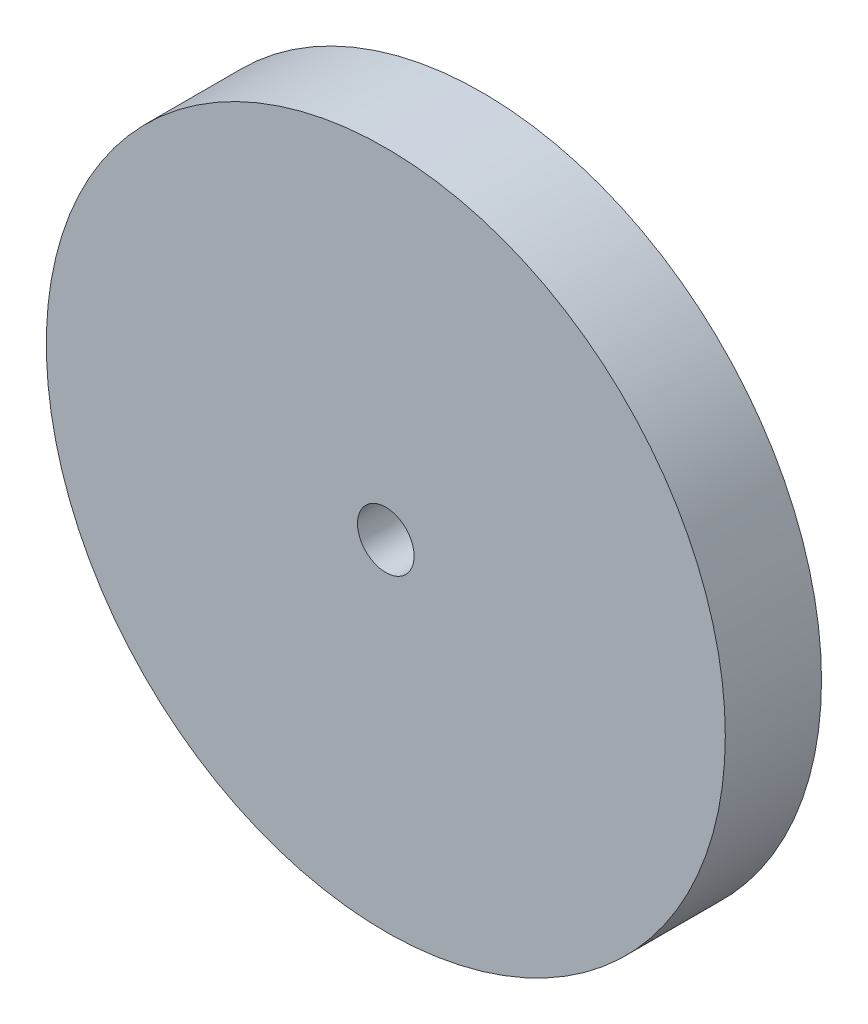
SolidWorks part; units mm, degrees
ref_plane "Front Plane" through (0, 0, 0) normal (0, 0, 1) x (1, 0, 0)
ref_plane "Top Plane" through (0, 0, 0) normal (0, 1, 0) x (1, 0, 0)
ref_plane "Right Plane" through (0, 0, 0) normal (1, 0, 0) x (0, 0, -1)
sketch "Sketch1" plane through (0, 0, 0) normal (0, 0, 1) x (1, 0, 0)
  circle A0 centre (0, 0) radius 30
  dimension "D1" = 60
extrude "Boss-Extrude1" add sketch "Sketch1" along normal blind 8.5
sketch "Sketch2" plane through (0, 0, 0) normal (0, 0, -1) x (-1, 0, 0)
  circle A0 centre (0, 0) radius 6
  circle A1 centre (0, 0) radius 2.5
  dimension "D1" = 5
  dimension "D2" = 12
extrude "Boss-Extrude2" add sketch "Sketch2" along normal blind 10
sketch "Sketch3" plane through (0, 0, -10) normal (0, 0, -1) x (-1, 0, 0)
  circle A0 centre (0, 0) radius 2.5
  circle A1 centre (0, 0) radius 2.5 construction
extrude "Cut-Extrude1" cut sketch "Sketch3" against normal through all
